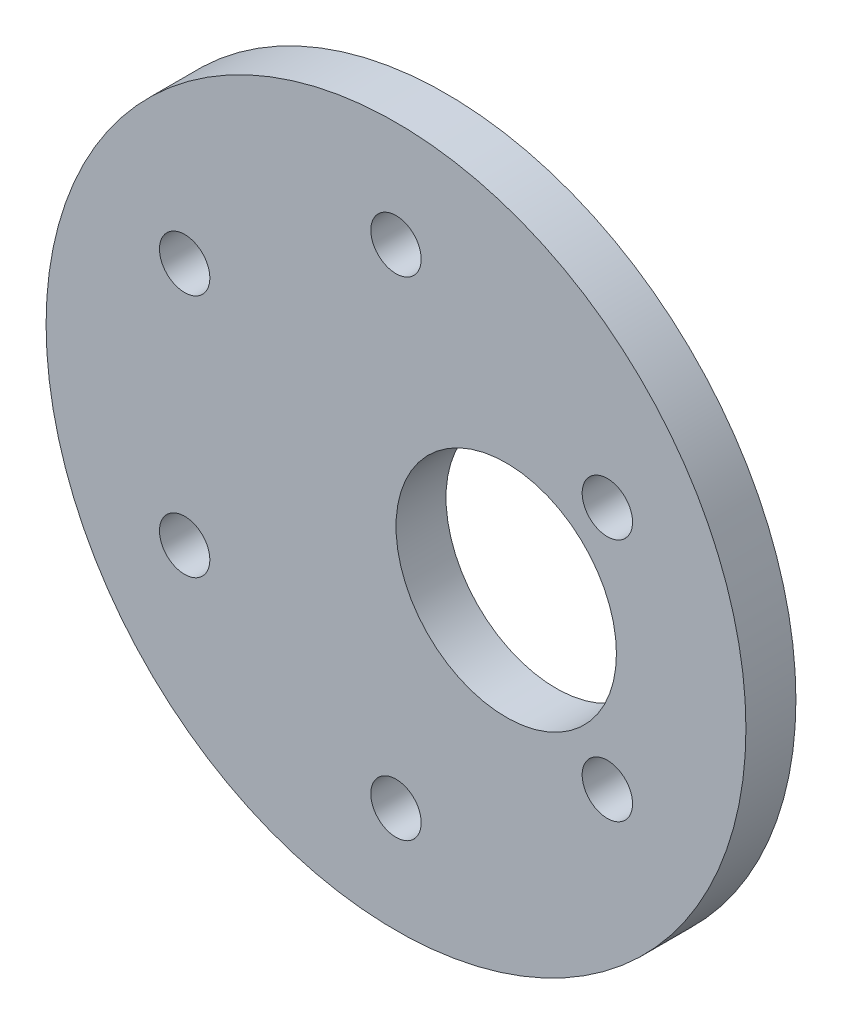
SolidWorks part; units mm, degrees
ref_plane "Front Plane" through (0, 0, 0) normal (0, 0, 1) x (1, 0, 0)
ref_plane "Top Plane" through (0, 0, 0) normal (0, 1, 0) x (1, 0, 0)
ref_plane "Right Plane" through (0, 0, 0) normal (1, 0, 0) x (0, 0, -1)
sketch "Sketch1" plane through (0, 0, 0) normal (0, 0, 1) x (1, 0, 0)
  line L1 (0, -15.5) -> (13.4234, -7.75) construction
  line L2 (13.4234, -7.75) -> (13.4234, 7.75) construction
  line L3 (13.4234, 7.75) -> (0, 15.5) construction
  line L4 (0, 15.5) -> (-13.4234, 7.75) construction
  line L5 (-13.4234, 7.75) -> (-13.4234, -7.75) construction
  line L6 (-13.4234, -7.75) -> (0, -15.5) construction
  circle A0 centre (0, 0) radius 18.4 construction
  circle A1 centre (0, 0) radius 13.4234 construction
  circle A2 centre (0, 0) radius 22.225
  dimension "D1" = 36.8
  dimension "D3" = 44.45
  dimension "D2" = 15.5
extrude "Boss-Extrude1" add sketch "Sketch1" along normal blind 3.175
hole_wizard "M3 Clearance Hole1" positions "Sketch3" profile "Sketch2" hole size "M3" standard "Ansi Metric" end condition up to next
sketch "Sketch3" plane through (0, 0, 3.175) normal (0, 0, 1) x (1, 0, 0)
  point P0 (-13.4234, 7.75)
  point P1 (0, 15.5)
  point P9 (13.4234, 7.75)
  point P12 (13.4234, -7.75)
  point P15 (0, -15.5)
  point P18 (-13.4234, -7.75)
sketch "Sketch2" plane through (-13.4234, 7.75, 3.175) normal (1, 0, 0) x (0, -1, 0)
  line L0 (0, 0) -> (0, 3.175)
  line L1 (0, 3.175) -> (1.6, 3.175)
  line L2 (1.6, 3.175) -> (1.6, 0)
  line L5 (1.6, 0) -> (0, 0)
  line L11 (0, -6.35) -> (0, 107.95) construction
  dimension "Thru Hole Dia." = 3.2
  dimension "Thru Hole Depth" = 3.175
sketch "Sketch4" plane through (0, 0, 3.175) normal (0, 0, 1) x (1, 0, 0)
  circle A0 centre (7, 0) radius 7
  dimension "D1" = 7
extrude "Cut-Extrude1" cut sketch "Sketch4" against normal up to next
